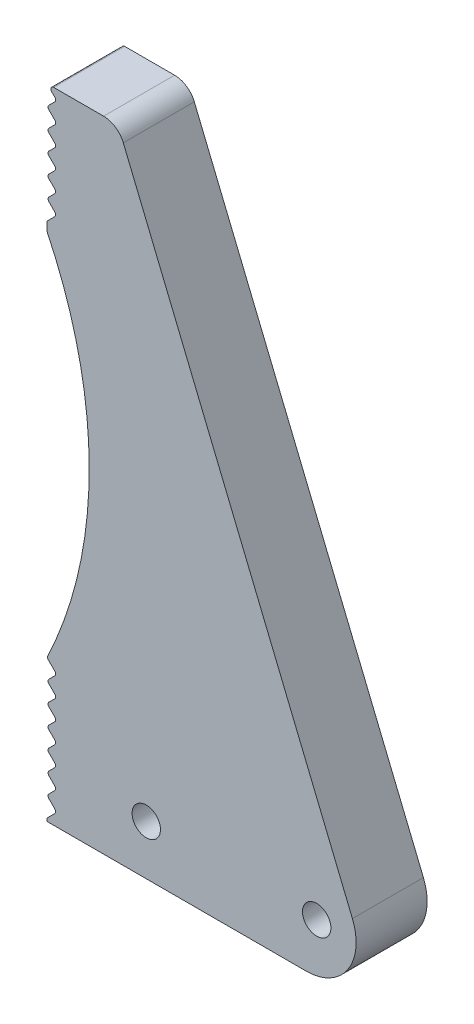
SolidWorks part; units mm, degrees
ref_plane "Front Plane" through (0, 0, 0) normal (0, 0, 1) x (1, 0, 0)
ref_plane "Top Plane" through (0, 0, 0) normal (0, 1, 0) x (1, 0, 0)
ref_plane "Right Plane" through (0, 0, 0) normal (1, 0, 0) x (0, 0, -1)
sketch "Sketch1" plane through (0, 0, 0) normal (0, 0, 1) x (1, 0, 0)
  line L0 (-30.5226, 36.1804) -> (-30.5226, 45.1804)
  line L1 (-30.5226, 45.1804) -> (-25.5226, 45.1804)
  line L2 (-25.5226, 45.1804) -> (-7.0226, 0.1804)
  line L3 (-7.0226, 0.1804) -> (-30.5226, 0.1804)
  line L4 (-30.5226, 0.1804) -> (-30.5226, 10.1804)
  arc A0 (-30.5226, 36.1804) -> (-30.5226, 10.1804) centre (-57.3646, 23.1804) cw
  circle A1 centre (-23.5226, 3.6804) radius 1
  circle A2 centre (-11.5226, 3.6804) radius 1
  dimension "D6" = 2
  dimension "D1" = 45
  dimension "D2" = 10
  dimension "D3" = 9
  dimension "D4" = 5
  dimension "D5" = 23.5
  dimension "D7" = 7
  dimension "D8" = 12
  dimension "D9" = 3.5
  dimension "D10" = 3.5
extrude "Extrude2" add sketch "Sketch1" along normal blind 5
fillet "Fillet2" radius 3.5 1 edges at (-7.0226, 0.1804, 2.5)
fillet "Fillet3" radius 1.5 1 edges at (-25.5226, 45.1804, 2.5)
sketch "Sketch3" plane through (0, 0, 5) normal (0, 0, 1) x (1, 0, 0)
  line L0 (-30.5226, 45.1804) -> (-29.8226, 44.4804)
  line L1 (-29.8226, 44.4804) -> (-30.5226, 43.7804)
  line L2 (-30.5226, 45.1804) -> (-30.5226, 36.1804) construction
  line L3 (-30.5226, 43.7804) -> (-29.8226, 43.0804)
  line L4 (-29.8226, 43.0804) -> (-30.5226, 42.3804)
  line L5 (-30.5226, 42.3804) -> (-29.8226, 41.6804)
  line L6 (-29.8226, 41.6804) -> (-30.5226, 40.9804)
  line L7 (-30.5226, 40.9804) -> (-29.8226, 40.2804)
  line L8 (-29.8226, 40.2804) -> (-30.5226, 39.5804)
  line L9 (-30.5226, 39.5804) -> (-29.8226, 38.8804)
  line L10 (-29.8226, 38.8804) -> (-30.5226, 38.1804)
  line L11 (-30.5226, 38.1804) -> (-29.8226, 37.4804)
  line L12 (-29.8226, 37.4804) -> (-30.5226, 36.7804)
  line L13 (-30.5226, 45.1804) -> (-30.5226, 36.7804)
  line M17 (-30.5226, 45.1804) -> (-30.5226, 36.1804)
  dimension "D1" = 1.4
extrude "Extrude4" cut sketch "Sketch3" against normal blind 5 contours L4 L3 M17 | L1 L0 M17 | L6 L5 M17 | L8 L7 M17 | L10 L9 M17 | L12 L11 M17
fillet "Fillet4" radius 0.2 13 edges at (-29.8226, 44.4804, 2.5) (-29.8226, 43.0804, 2.5) (-29.8226, 41.6804, 2.5) (-29.8226, 40.2804, 2.5) (-29.8226, 38.8804, 2.5) (-29.8226, 37.4804, 2.5) (-30.5226, 36.7804, 2.5) (-30.5226, 38.1804, 2.5) (-30.5226, 39.5804, 2.5) (-30.5226, 40.9804, 2.5) (-30.5226, 42.3804, 2.5) (-30.5226, 43.7804, 2.5) (-30.5226, 45.1804, 2.5)
sketch "Sketch4" plane through (0, 0, 5) normal (0, 0, 1) x (1, 0, 0)
  line L0 (-30.5226, 10.1804) -> (-29.8226, 9.4804)
  line L1 (-29.8226, 9.4804) -> (-30.5226, 8.7804)
  line L2 (-30.5226, 10.1804) -> (-30.5226, 0.1804) construction
  line L3 (-30.5226, 8.7804) -> (-29.8226, 8.0804)
  line L4 (-29.8226, 8.0804) -> (-30.5226, 7.3804)
  line L5 (-30.5226, 7.3804) -> (-29.8226, 6.6804)
  line L6 (-29.8226, 6.6804) -> (-30.5226, 5.9804)
  line L7 (-30.5226, 5.9804) -> (-29.8226, 5.2804)
  line L8 (-29.8226, 5.2804) -> (-30.5226, 4.5804)
  line L9 (-30.5226, 4.5804) -> (-29.8226, 3.8804)
  line L10 (-29.8226, 3.8804) -> (-30.5226, 3.1804)
  line L11 (-30.5226, 3.1804) -> (-29.8226, 2.4804)
  line L12 (-29.8226, 2.4804) -> (-30.5226, 1.7804)
  line L13 (-30.5226, 1.7804) -> (-29.8226, 1.0804)
  line L14 (-29.8226, 1.0804) -> (-30.5226, 0.3804)
  line L15 (-30.5226, 10.1804) -> (-30.5226, 0.3804)
  line M7 (-30.5226, 10.1804) -> (-30.5226, 0.1804)
  dimension "D1" = 1.4
extrude "Extrude5" cut sketch "Sketch4" against normal blind 5 contours L14 L13 M7 | L12 L11 M7 | L10 L9 M7 | L8 L7 M7 | L6 L5 M7 | L4 L3 M7 | L1 L0 M7
fillet "Fillet5" radius 0.2 15 edges at (-30.5226, 0.3804, 2.5) (-29.8226, 1.0804, 2.5) (-30.5226, 1.7804, 2.5) (-29.8226, 2.4804, 2.5) (-30.5226, 3.1804, 2.5) (-29.8226, 3.8804, 2.5) (-30.5226, 4.5804, 2.5) (-29.8226, 5.2804, 2.5) (-30.5226, 5.9804, 2.5) (-29.8226, 6.6804, 2.5) (-30.5226, 7.3804, 2.5) (-29.8226, 8.0804, 2.5) (-30.5226, 8.7804, 2.5) (-29.8226, 9.4804, 2.5) (-30.5226, 10.1804, 2.5)
